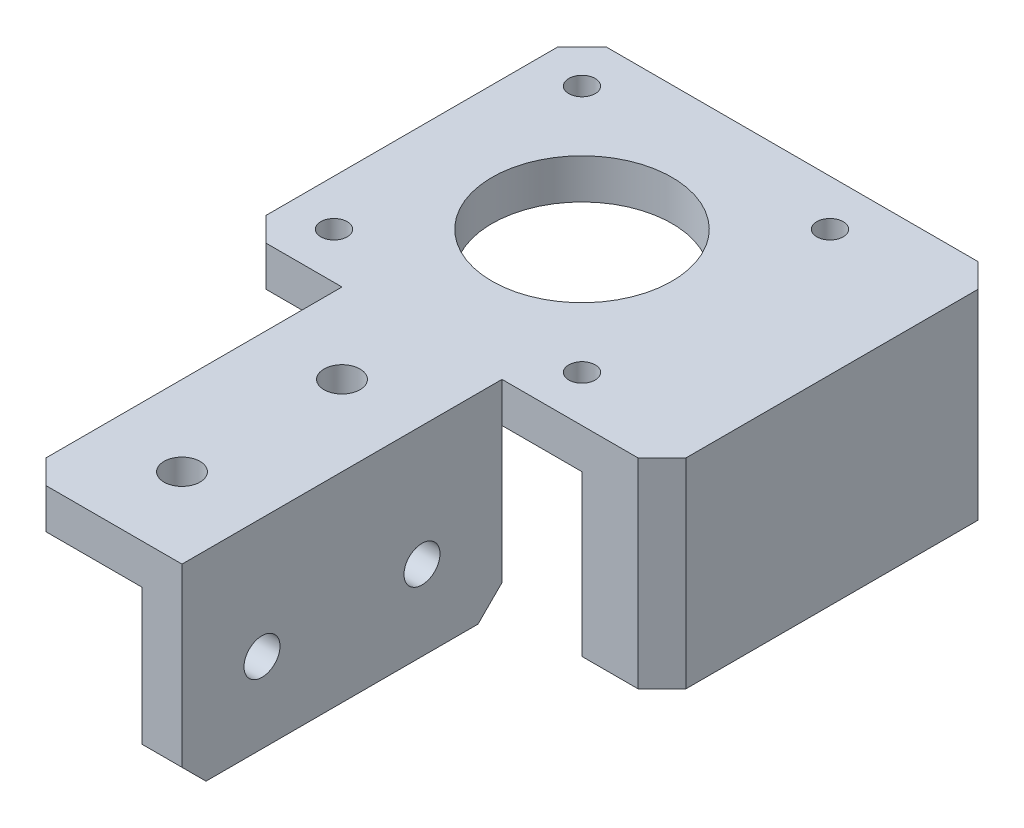
SolidWorks part; units mm, degrees
ref_plane "Front Plane" through (0, 0, 0) normal (0, 0, 1) x (1, 0, 0)
ref_plane "Top Plane" through (0, 0, 0) normal (0, 1, 0) x (1, 0, 0)
ref_plane "Right Plane" through (0, 0, 0) normal (1, 0, 0) x (0, 0, -1)
sketch "Sketch1" plane through (0, 0, 0) normal (0, 1, 0) x (1, 0, 0)
  line L0 (-21.25, 0) -> (21.25, 0) construction
  line L1 (-21.25, -21.25) -> (21.25, -21.25)
  line L2 (-21.25, -21.25) -> (-21.25, 21.25)
  line L3 (-21.25, 21.25) -> (21.25, 21.25)
  line L4 (21.25, -21.25) -> (21.25, 21.25)
  line L5 (-21.25, -21.25) -> (21.25, 21.25) construction
  line L6 (-21.25, 21.25) -> (21.25, -21.25) construction
  line L7 (0, 21.25) -> (0, -21.25) construction
  circle A0 centre (0, 0) radius 11.25
  circle A1 centre (-15.5, 15.5) radius 1.65
  circle A2 centre (15.5, 15.5) radius 1.65
  circle A3 centre (15.5, -15.5) radius 1.65
  circle A4 centre (-15.5, -15.5) radius 1.65
  dimension "D1" = 22.5
  dimension "D4" = 15.5
  dimension "D5" = 15.5
  dimension "D6" = 3.3
  dimension "D2" = 42.5
  dimension "D3" = 42.5
extrude "Boss-Extrude1" add sketch "Sketch1" along normal blind 5
sketch "Sketch3" plane through (0, 5, 0) normal (0, 1, 0) x (1, 0, 0)
  line L0 (21.25, 21.25) -> (31.25, 21.25) construction
  line L10 (-21.25, -21.25) -> (21.25, -21.25) construction
  line L11 (21.25, -21.25) -> (31.25, -21.25)
  line L12 (21.25, -21.25) -> (21.25, 21.25)
  line L13 (21.25, 21.25) -> (31.25, 21.25)
  line L14 (31.25, -21.25) -> (31.25, 21.25)
  line L15 (6.25, -21.25) -> (11.25, -21.25)
  line L16 (6.25, -21.25) -> (6.25, -61.25)
  line L17 (6.25, -61.25) -> (11.25, -61.25)
  line L18 (11.25, -21.25) -> (11.25, -61.25)
  dimension "D1" = 10
  dimension "D2" = 5
  dimension "D3" = 40
  dimension "D4" = 10
extrude "Boss-Extrude2" add sketch "Sketch3" against normal blind 25
chamfer "Chamfer1" distance 3 angle 45 4 edges at (31.25, -7.5, -21.25) (31.25, -7.5, 21.25) (-21.25, 2.5, 21.25) (-21.25, 2.5, -21.25)
sketch "Sketch5" plane through (6.25, 0, 0) normal (-1, 0, 0) x (0, 0, 1)
  line L1 (21.25, 0) -> (61.25, 0)
  line L2 (21.25, 0) -> (21.25, 5)
  line L3 (21.25, 5) -> (61.25, 5)
  line L4 (61.25, 0) -> (61.25, 5)
extrude "Boss-Extrude3" add sketch "Sketch5" along normal blind 15
sketch "Sketch9" plane through (0, 5, 0) normal (0, 1, 0) x (1, 0, 0)
  line L0 (-8.75, -21.25) -> (11.25, -21.25) construction
  line L1 (1.25, -61.25) -> (1.25, -21.25) construction
  line L2 (-8.75, -61.25) -> (11.25, -61.25) construction
  line L3 (-8.75, -41.25) -> (11.25, -41.25) construction
  line L4 (-8.75, -61.25) -> (-8.75, -21.25) construction
  line L5 (11.25, -61.25) -> (11.25, -21.25) construction
  circle A0 centre (1.25, -51.25) radius 2.25
  circle A1 centre (1.25, -31.25) radius 2.25
  dimension "D1" = 10
  dimension "D2" = 4.5
extrude "Cut-Extrude5" cut sketch "Sketch9" against normal up to next
sketch "Sketch10" plane through (6.25, 0, 0) normal (-1, 0, 0) x (0, 0, 1)
  line L0 (21.25, -10) -> (61.25, -10) construction
  line L1 (21.25, -20) -> (21.25, 0) construction
  line L2 (61.25, -20) -> (61.25, 0) construction
  line L3 (41.25, -20) -> (41.25, 0) construction
  line L4 (21.25, -20) -> (61.25, -20) construction
  line L5 (21.25, 0) -> (61.25, 0) construction
  circle A0 centre (51.25, -10) radius 2.25
  circle A1 centre (31.25, -10) radius 2.25
  dimension "D1" = 4.5
  dimension "D2" = 10
extrude "Cut-Extrude6" cut sketch "Sketch10" against normal up to next
sketch "Sketch11" plane through (0, 0, 0) normal (0, -1, 0) x (1, 0, 0)
  circle A0 centre (1.25, 51.25) radius 3.75
  circle A1 centre (1.25, 31.25) radius 3.75
  dimension "D1" = 7.5
  dimension "D3" = 20
  dimension "D2" = 2
extrude "Cut-Extrude7" cut sketch "Sketch11" against normal blind 1
sketch "Sketch12" plane through (6.25, 0, 0) normal (-1, 0, 0) x (0, 0, 1)
  circle A0 centre (31.25, -10) radius 3.75
  circle A1 centre (51.25, -10) radius 3.75
  dimension "D1" = 7.5
  dimension "D3" = 20
  dimension "D2" = 2
extrude "Cut-Extrude8" cut sketch "Sketch12" against normal blind 1
chamfer "Chamfer2" distance 3 angle 45 3 edges at (-8.75, 2.5, 61.25) (8.75, -20, 61.25) (8.75, -20, 21.25)
